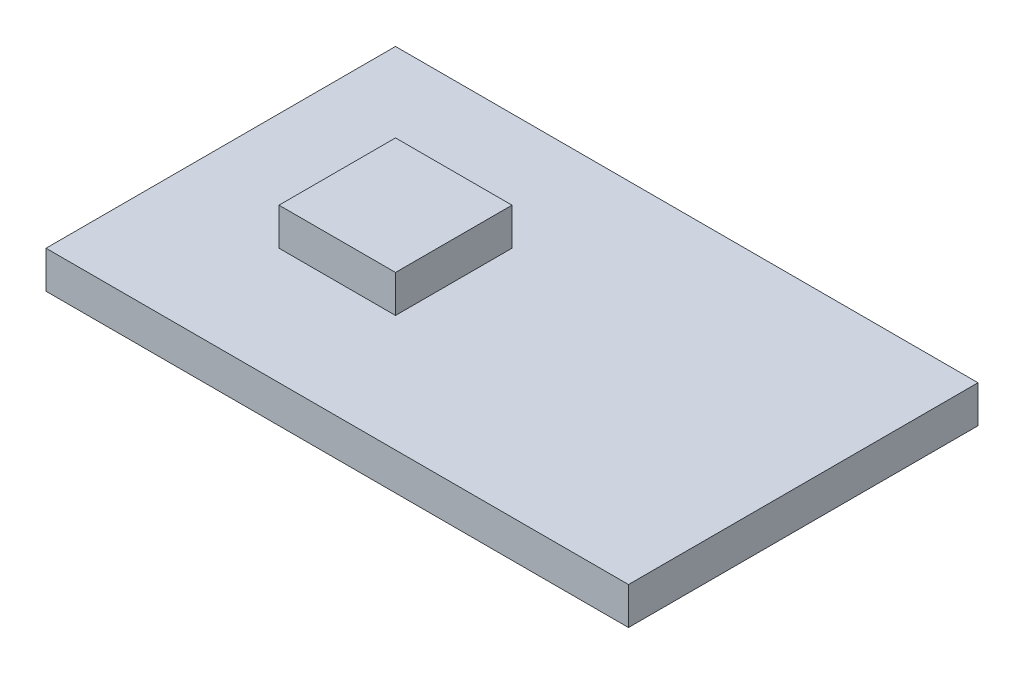
SolidWorks part; units mm, degrees
ref_plane "Front Plane" through (0, 0, 0) normal (0, 0, 1) x (1, 0, 0)
ref_plane "Top Plane" through (0, 0, 0) normal (0, 1, 0) x (1, 0, 0)
ref_plane "Right Plane" through (0, 0, 0) normal (1, 0, 0) x (0, 0, -1)
sketch "Sketch1" plane through (0, 0, 0) normal (0, 1, 0) x (1, 0, 0)
  line L1 (-7.9375, -4.7625) -> (7.9375, -4.7625)
  line L2 (-7.9375, -4.7625) -> (-7.9375, 4.7625)
  line L3 (-7.9375, 4.7625) -> (7.9375, 4.7625)
  line L4 (7.9375, -4.7625) -> (7.9375, 4.7625)
  line L5 (-7.9375, -4.7625) -> (7.9375, 4.7625) construction
  line L6 (-7.9375, 4.7625) -> (7.9375, -4.7625) construction
  point P0 (0, 0)
  dimension "D1" = 9.525
  dimension "D2" = 15.875
extrude "Extrude1" add sketch "Sketch1" along normal blind 1.016
sketch "Sketch2" plane through (0, 1.016, 0) normal (0, 1, 0) x (-1, 0, 0)
  line L0 (7.9375, -4.7625) -> (7.9375, 4.7625) construction
  line L1 (4.7625, 1.5875) -> (1.5875, 1.5875)
  line L2 (4.7625, 1.5875) -> (4.7625, -1.5875)
  line L3 (4.7625, -1.5875) -> (1.5875, -1.5875)
  line L4 (1.5875, 1.5875) -> (1.5875, -1.5875)
  line L5 (4.7625, 1.5875) -> (1.5875, -1.5875) construction
  line L6 (4.7625, -1.5875) -> (1.5875, 1.5875) construction
  point P0 (3.175, 0)
  dimension "D1" = 3.175
  dimension "D2" = 3.175
  dimension "D3" = 3.175
extrude "Extrude2" add sketch "Sketch2" along normal blind 1.016
